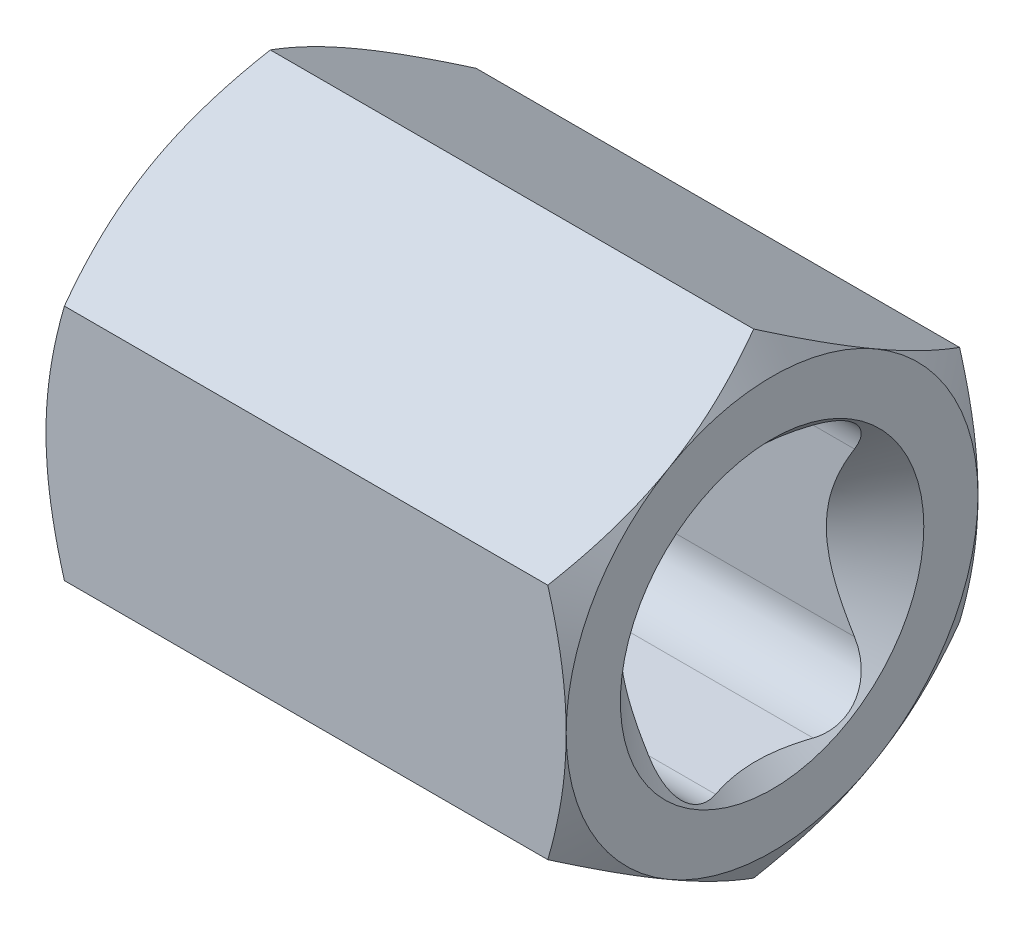
SolidWorks part; units mm, degrees
ref_plane "Plan de face" through (0, 0, 0) normal (0, 0, 1) x (1, 0, 0)
ref_plane "Plan de dessus" through (0, 0, 0) normal (0, 1, 0) x (1, 0, 0)
ref_plane "Plan de droite" through (0, 0, 0) normal (1, 0, 0) x (0, 0, -1)
sketch "Esquisse1" plane through (0, 0, 0) normal (1, 0, 0) x (0, 0, -1)
  line L0 (0, 16.0615) -> (0, -16.0615) construction
  line L1 (16.9846, 0) -> (-16.9846, 0) construction
  line L2 (2.25, 6.25) -> (-2.25, 6.25)
  line L3 (4.75, 3.75) -> (4.75, -3.75)
  line L4 (-4.75, 3.75) -> (-4.75, -3.75)
  line L5 (2.25, -6.25) -> (-2.25, -6.25)
  line L6 (4.75, 6.25) -> (-4.75, -6.25) construction
  line L7 (-4.75, 6.25) -> (4.75, -6.25) construction
  line L8 (-9.5, -5.4848) -> (-9.5, 5.4848)
  line L9 (-9.5, 5.4848) -> (0, 10.9697)
  line L10 (0, 10.9697) -> (9.5, 5.4848)
  line L11 (9.5, 5.4848) -> (9.5, -5.4848)
  line L12 (9.5, -5.4848) -> (0, -10.9697)
  line L13 (0, -10.9697) -> (-9.5, -5.4848)
  line L14 (-4.5, 3.9686) -> (-4.5, -3.9686)
  line L16 (4.5, -3.9686) -> (4.5, 3.9686)
  circle A0 centre (0, 0) radius 9.5 construction
  arc A1 (4.5, 3.9686) -> (-4.5, 3.9686) centre (0, 0) ccw
  arc A2 (-4.5, -3.9686) -> (4.5, -3.9686) centre (0, 0) ccw
  arc A3 (-4.75, -3.75) -> (-2.25, -6.25) centre (-2.25, -3.75) ccw
  arc A4 (4.75, -3.75) -> (2.25, -6.25) centre (2.25, -3.75) cw
  arc A5 (4.75, 3.75) -> (2.25, 6.25) centre (2.25, 3.75) ccw
  arc A6 (-2.25, 6.25) -> (-4.75, 3.75) centre (-2.25, 3.75) ccw
  point P4 (0, 0)
  point P8 (0, 0)
  point P9 (0, 0)
  point P23 (0, 0)
  dimension "D3" = 9
  dimension "D5" = 6
  dimension "D6" = 2.5
  dimension "D1" = 12.5
  dimension "D2" = 9.5
  dimension "D4" = 4.5
  dimension "D7" = 19
extrude "Boss.-Extru.1" add sketch "Esquisse1" along normal blind 24 contours L9 L10 L11 L12 L13 L8 | A6 L4 A3 L5 A4 L3 A5 L2
sketch "Esquisse3" plane through (24, 0, 0) normal (1, 0, 0) x (0, 0, -1)
  line L0 (-9.5, 0) -> (9.5, 0) construction
  line L1 (-9.5, -5.4848) -> (-9.5, 5.4848) construction
  line L2 (9.5, 5.4848) -> (9.5, -5.4848) construction
sketch "Esquisse4" plane through (0, 0, 0) normal (-1, 0, 0) x (0, 0, 1)
  line L0 (-9.5, 0) -> (9.5, 0) construction
  line L1 (-9.5, 5.4848) -> (-9.5, -5.4848) construction
  line L2 (9.5, -5.4848) -> (9.5, 5.4848) construction
sketch "Esquisse5" plane through (0, 0, 0) normal (0, 1, 0) x (1, 0, 0)
  line L0 (24, 0) -> (0, 0) construction
  line L1 (24, -9.5) -> (24, 9.5) construction
sketch "Esquisse6" plane through (0, 0, 0) normal (0, 1, 0) x (1, 0, 0)
  line L0 (-4.4843, 1.7329) -> (2.7602, 14.2807)
  line L1 (28.0088, 15.5409) -> (-4.4843, 15.5409)
  line L2 (-4.4843, 15.5409) -> (-4.4843, 1.7329)
  line L4 (2.7602, 14.2807) -> (21.2398, 14.2807)
  line L5 (21.2398, 14.2807) -> (28.0088, 2.5566)
  line L6 (28.0088, 2.5566) -> (28.0088, 15.5409)
  dimension "D1" = 60
  dimension "D2" = 60
revolve "Enlèvement de matière-Révolution1" cut sketch "Esquisse6" angle 360 about L0
sketch "Esquisse11" plane through (0, 0, 0) normal (0, 1, 0) x (1, 0, 0)
  line L0 (0, 0) -> (0, -7)
  line L1 (0, 9.5) -> (0, -9.5) construction
  line L2 (0, -7) -> (3, -4)
  line L3 (3, -4) -> (21, -4)
  line L4 (21, -4) -> (24, -7)
  line L5 (24, -9.5) -> (24, 9.5) construction
  line L6 (24, -7) -> (24, 0)
  line L7 (24, 0) -> (0, 0)
  dimension "D1" = 45
  dimension "D2" = 45
  dimension "D3" = 7
  dimension "D4" = 4
  dimension "D5" = 7
revolve "Enlèvement de matière-Révolution3" cut sketch "Esquisse11" angle 360 about L0
